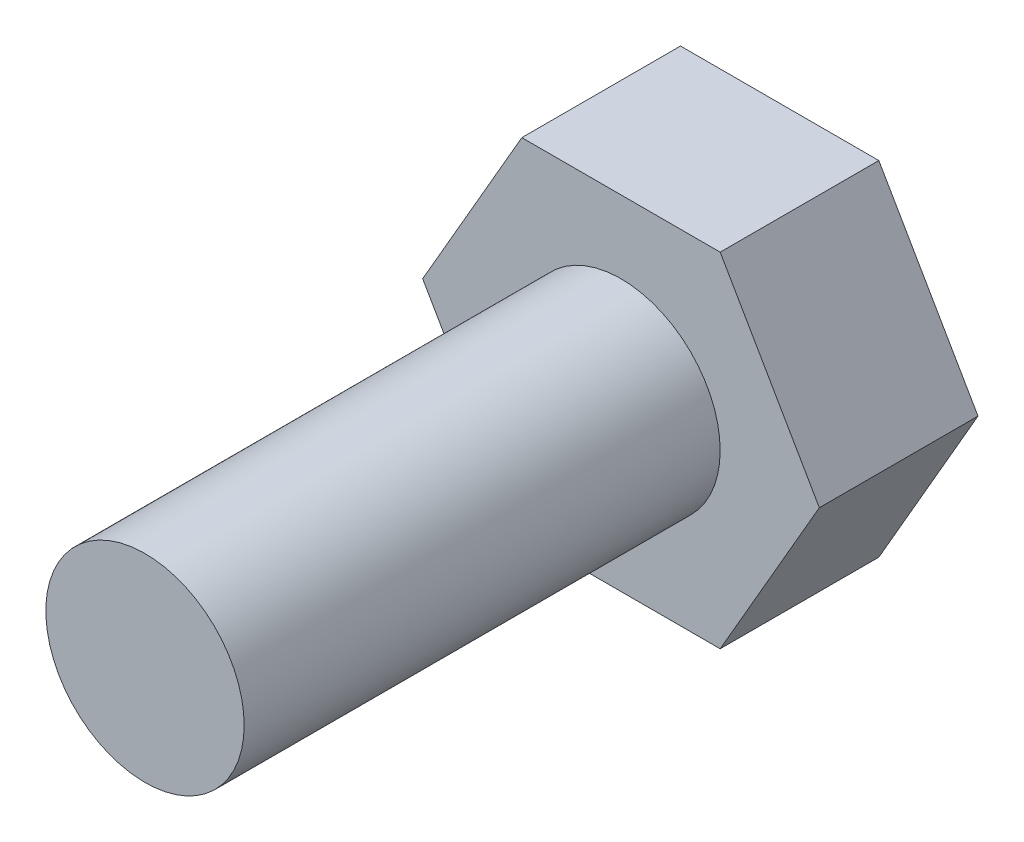
SolidWorks part; units mm, degrees
ref_plane "Alzado" through (0, 0, 0) normal (0, 0, 1) x (1, 0, 0)
ref_plane "Planta" through (0, 0, 0) normal (0, 1, 0) x (1, 0, 0)
ref_plane "Vista lateral" through (0, 0, 0) normal (1, 0, 0) x (0, 0, -1)
sketch "Croquis2" plane through (0, 0, 0) normal (0, 0, 1) x (1, 0, 0)
  circle A0 centre (0, 0) radius 2.5
extrude "Saliente-Extruir1" add sketch "Croquis2" along normal blind 12
sketch "Croquis3" plane through (0, 0, 0) normal (0, 0, -1) x (-1, 0, 0)
  line L1 (5, 0) -> (2.5, 4.3301)
  line L2 (2.5, 4.3301) -> (-2.5, 4.3301)
  line L3 (-2.5, 4.3301) -> (-5, 0)
  line L4 (-5, 0) -> (-2.5, -4.3301)
  line L5 (-2.5, -4.3301) -> (2.5, -4.3301)
  line L6 (2.5, -4.3301) -> (5, 0)
  circle A1 centre (0, 0) radius 4.3301 construction
  dimension "D1" = 5
extrude "Saliente-Extruir3" add sketch "Croquis3" along normal blind 4
